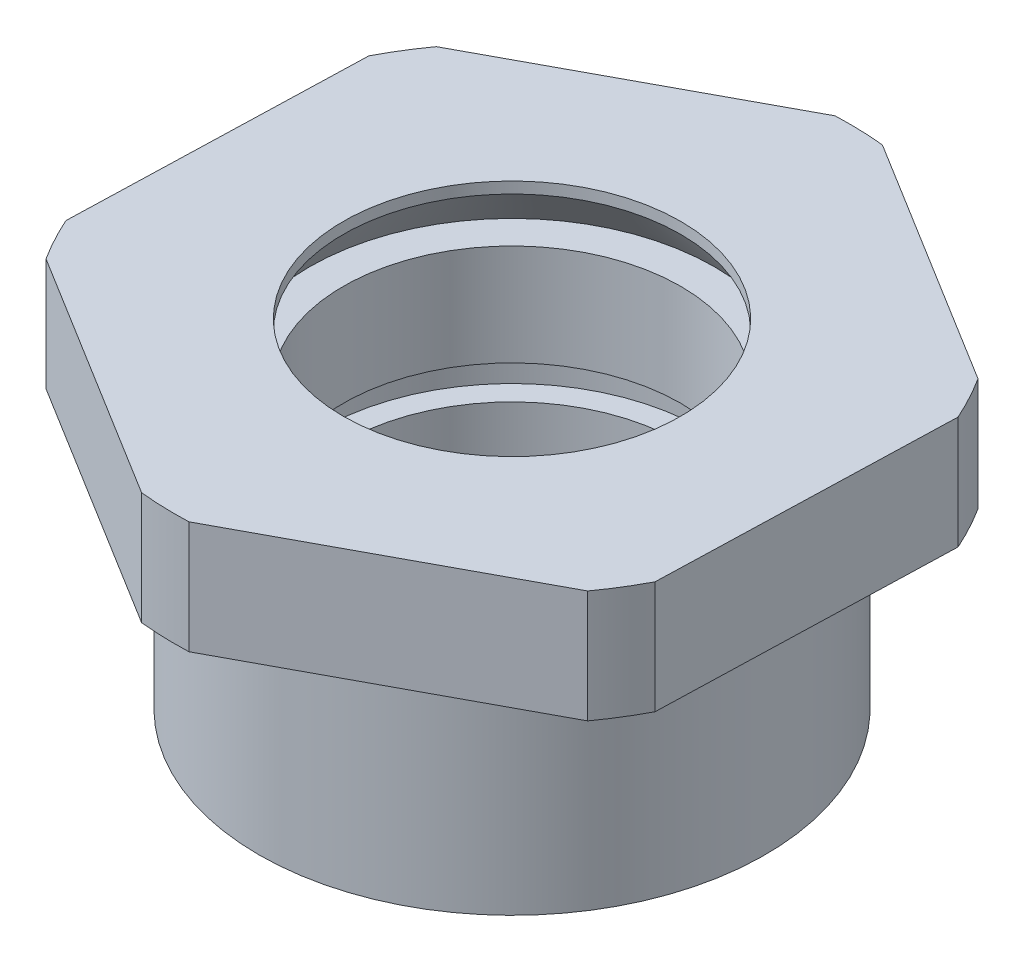
SolidWorks part; units mm, degrees
ref_plane "Front Plane" through (0, 0, 0) normal (0, 0, 1) x (1, 0, 0)
ref_plane "Top Plane" through (0, 0, 0) normal (0, 1, 0) x (1, 0, 0)
ref_plane "Right Plane" through (0, 0, 0) normal (1, 0, 0) x (0, 0, -1)
sketch "Sketch2" plane through (0, 0, 0) normal (0, 0, 1) x (1, 0, 0)
  line L0 (0, 16.3065) -> (0, 0) construction
  line L1 (0, 0) -> (19.7419, 0) construction
  line L2 (22.5, 0) -> (22.5, 17)
  line L3 (22.5, 17) -> (21, 17)
  line L4 (21, 17) -> (21, 20)
  line L5 (21, 20) -> (30, 20)
  line L6 (30, 20) -> (30, 30)
  line L7 (30, 30) -> (15, 30)
  line L8 (15, 30) -> (15, 29)
  line L9 (15, 29) -> (18, 25)
  line L10 (18, 25) -> (15, 25)
  line L14 (17, 13) -> (15, 13)
  line L15 (15, 13) -> (15, 8)
  line L16 (15, 8) -> (17, 8)
  line L17 (17, 8) -> (17, 5)
  line L18 (17, 5) -> (15, 5)
  line L19 (15, 5) -> (15, 0)
  line L20 (15, 0) -> (22.5, 0)
  line L21 (17, 13) -> (17, 16)
  line L22 (17, 16) -> (15, 16)
  line L23 (15, 16) -> (15, 25)
  point P10 (0, 0)
  point P20 (21, 18.5)
  dimension "D1" = 3
  dimension "D2" = 5
  dimension "D3" = 3
  dimension "D4" = 1
  dimension "D5" = 4
  dimension "D6" = 10
  dimension "D7" = 20
  dimension "D8" = 21
  dimension "D9" = 30
  dimension "D10" = 22.5
  dimension "D11" = 15
  dimension "D12" = 3
  dimension "D13" = 17
  dimension "D14" = 3
  dimension "D15" = 5
revolve "Revolve1" add sketch "Sketch2" angle 360 about L0
sketch "Sketch3" plane through (0, 30, 0) normal (0, 1, 0) x (1, 0, 0)
  line L1 (0.9361, 31.1629) -> (-26.5198, 16.3921)
  line L2 (-26.5198, 16.3921) -> (-27.4559, -14.7708)
  line L3 (-27.4559, -14.7708) -> (-0.9361, -31.1629)
  line L4 (-0.9361, -31.1629) -> (26.5198, -16.3921)
  line L5 (26.5198, -16.3921) -> (27.4559, 14.7708)
  line L6 (27.4559, 14.7708) -> (0.9361, 31.1629)
  circle A0 centre (0, 0) radius 27 construction
  circle A1 centre (0, 0) radius 30 construction
  dimension "D1" = 3
extrude "Cut-Extrude1" cut sketch "Sketch3" against normal through all flip side to cut
